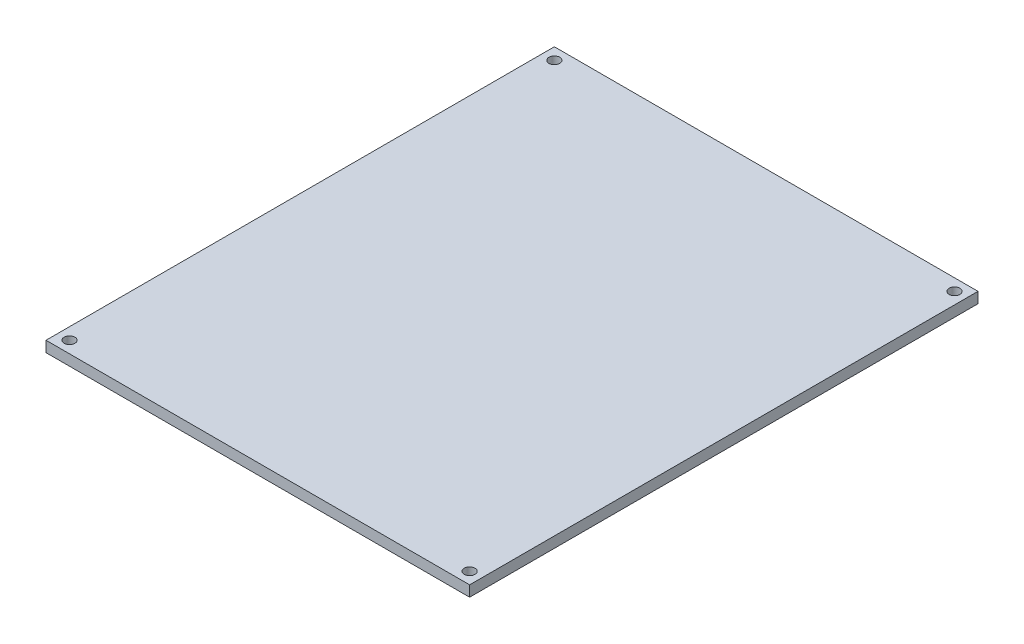
SolidWorks part; units mm, degrees
ref_plane "Front Plane" through (0, 0, 0) normal (0, 0, 1) x (1, 0, 0)
ref_plane "Top Plane" through (0, 0, 0) normal (0, 1, 0) x (1, 0, 0)
ref_plane "Right Plane" through (0, 0, 0) normal (1, 0, 0) x (0, 0, -1)
sketch "Sketch1" plane through (0, 0, 0) normal (0, 1, 0) x (1, 0, 0)
  line L1 (0, 0) -> (100, 0)
  line L2 (0, 0) -> (0, 120)
  line L3 (0, 120) -> (100, 120)
  line L4 (100, 0) -> (100, 120)
  dimension "D1" = 100
  dimension "D2" = 120
extrude "Boss-Extrude1" add sketch "Sketch1" along normal blind 2.54
sketch "Sketch2" plane through (0, 2.54, 0) normal (0, 1, 0) x (1, 0, 0)
  line L0 (0, 120) -> (0, 0) construction
  line L1 (100, 120) -> (0, 120) construction
  line L2 (100, 0) -> (100, 120) construction
  line L3 (0, 0) -> (100, 0) construction
  circle A0 centre (2.7745, 117.2255) radius 1.27
  circle A1 centre (97.2255, 117.2255) radius 1.27
  circle A2 centre (97.2255, 2.7745) radius 1.27
  circle A3 centre (2.7745, 2.7745) radius 1.27
  point P16 (0, 0)
  dimension "D1" = 2.54
  dimension "D2" = 2.7745
  dimension "D3" = 2.7745
  dimension "D4" = 2.7745
  dimension "D5" = 2.7745
extrude "Cut-Extrude1" cut sketch "Sketch2" against normal through all
